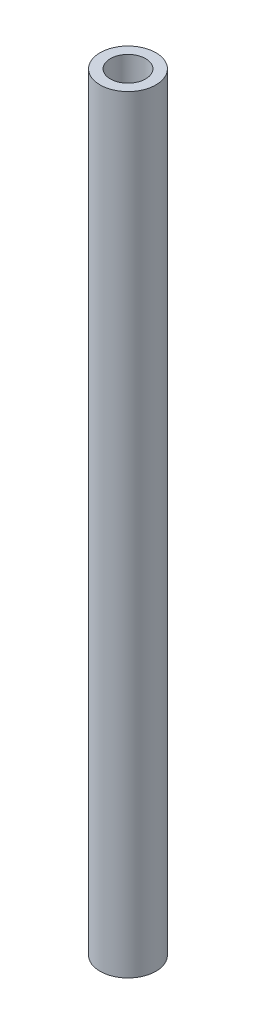
SolidWorks part; units mm, degrees
material "1060 Alloy"
ref_plane "Front Plane" through (0, 0, 0) normal (0, 0, 1) x (1, 0, 0)
ref_plane "Top Plane" through (0, 0, 0) normal (0, 1, 0) x (1, 0, 0)
ref_plane "Right Plane" through (0, 0, 0) normal (1, 0, 0) x (0, 0, -1)
sketch "Sketch2" plane through (0, 0, 0) normal (0, 1, 0) x (1, 0, 0)
  circle A0 centre (0, 0) radius 4
  dimension "D1" = 8
extrude "Boss-Extrude1" add sketch "Sketch2" against normal blind 110
hole_wizard "#8 (0.199) Diameter Hole3" positions "Sketch9" profile "Sketch8" hole size "#8" standard "ANSI Inch"
sketch "Sketch9" plane through (0, 0, 0) normal (0, 1, 0) x (1, 0, 0)
  point P0 (0, 0)
sketch "Sketch8" plane through (0, 0, 0) normal (1, 0, 0) x (0, 0, 1)
  line L0 (0, 0) -> (0, 11.5186)
  line L1 (0, 11.5186) -> (2.5273, 10)
  line L2 (2.5273, 10) -> (2.5273, 0)
  line L5 (2.5273, 0) -> (0, 0)
  line L10 (0, 11.5186) -> (-2.5273, 10) construction
  line L11 (0, -6.35) -> (0, 107.95) construction
  dimension "Hole Dia." = 5.0546
  dimension "Hole Depth" = 10
  dimension "Drill Angle" = 118
hole_wizard "#8 (0.199) Diameter Hole4" positions "Sketch11" profile "Sketch10" hole size "#8" standard "ANSI Inch"
sketch "Sketch11" plane through (0, -110, 0) normal (0, -1, 0) x (-1, 0, 0)
  point P0 (0, 0)
sketch "Sketch10" plane through (0, -110, 0) normal (1, 0, 0) x (0, 0, -1)
  line L0 (0, 0) -> (0, 11.5186)
  line L1 (0, 11.5186) -> (2.5273, 10)
  line L2 (2.5273, 10) -> (2.5273, 0)
  line L5 (2.5273, 0) -> (0, 0)
  line L10 (0, 11.5186) -> (-2.5273, 10) construction
  line L11 (0, -6.35) -> (0, 107.95) construction
  dimension "Hole Dia." = 5.0546
  dimension "Hole Depth" = 10
  dimension "Drill Angle" = 118
